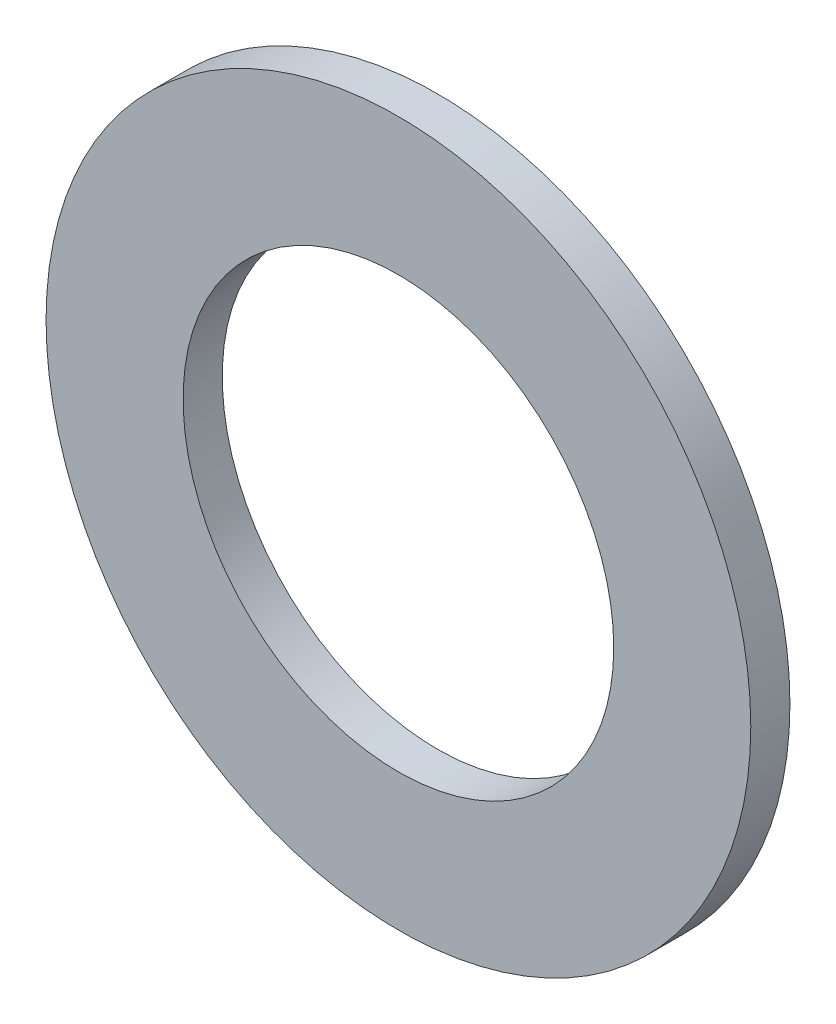
SolidWorks part; units mm, degrees
material "Картон"
ref_plane "Спереди" through (0, 0, 0) normal (0, 0, 1) x (1, 0, 0)
ref_plane "Сверху" through (0, 0, 0) normal (0, 1, 0) x (1, 0, 0)
ref_plane "Справа" through (0, 0, 0) normal (1, 0, 0) x (0, 0, -1)
sketch "Эскиз1" plane through (0, 0, 0) normal (0, 0, 1) x (1, 0, 0)
  circle A0 centre (0, 0) radius 22
  circle A1 centre (0, 0) radius 36
  dimension "D1" = 44
  dimension "D2" = 72
extrude "Бобышка-Вытянуть1" add sketch "Эскиз1" along normal blind 4
